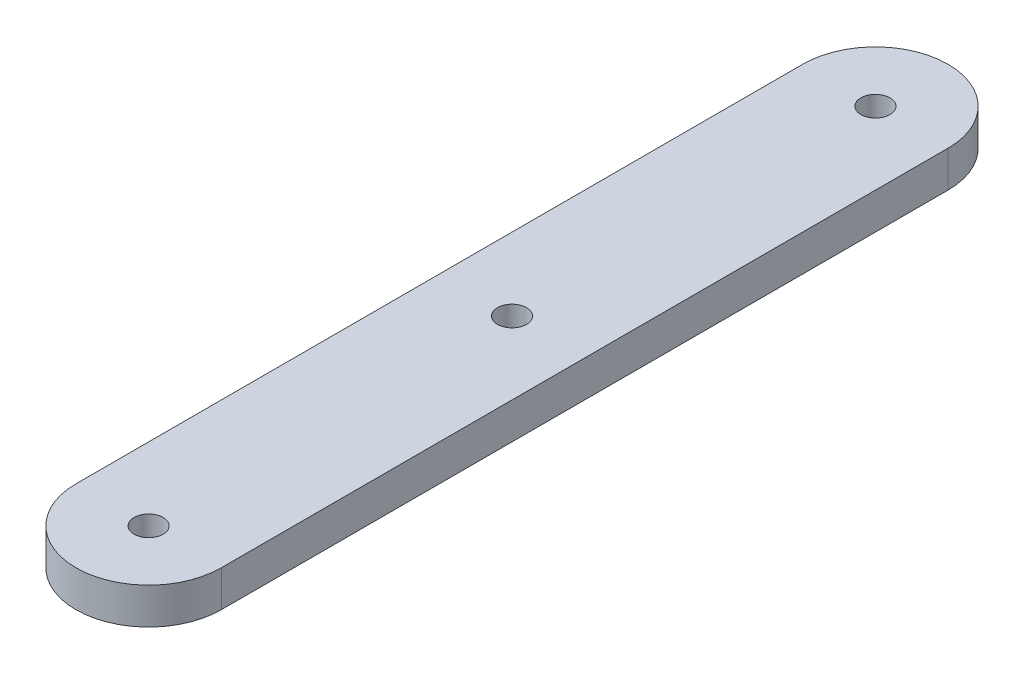
SolidWorks part; units mm, degrees
material "Polylactic Acid (PLA)"
ref_plane "Front Plane" through (0, 0, 0) normal (0, 0, 1) x (1, 0, 0)
ref_plane "Top Plane" through (0, 0, 0) normal (0, 1, 0) x (1, 0, 0)
ref_plane "Right Plane" through (0, 0, 0) normal (1, 0, 0) x (0, 0, -1)
sketch "Sketch2" plane through (0, 0, 0) normal (0, 1, 0) x (1, 0, 0)
  line L2 (-6.35, -31.75) -> (-6.35, 31.75)
  line L4 (6.35, -31.75) -> (6.35, 31.75)
  arc A0 (-6.35, 31.75) -> (6.35, 31.75) centre (0, 31.75) cw
  arc A1 (6.35, -31.75) -> (-6.35, -31.75) centre (0, -31.75) cw
  circle A2 centre (0, 31.75) radius 1.27
  circle A3 centre (0, -31.75) radius 1.27
  circle A4 centre (0, 0) radius 1.27
  dimension "D3" = 2.54
  dimension "D4" = 2.54
  dimension "D5" = 2.54
  dimension "D1" = 63.5
  dimension "D2" = 12.7
  dimension "D6" = 31.75
extrude "Boss-Extrude1" add sketch "Sketch2" along normal blind 3.175 contours A1 L4 A0 L2 A3 A2
equation "\"D6@Sketch2\"=\"D1@Sketch2\"/2"
